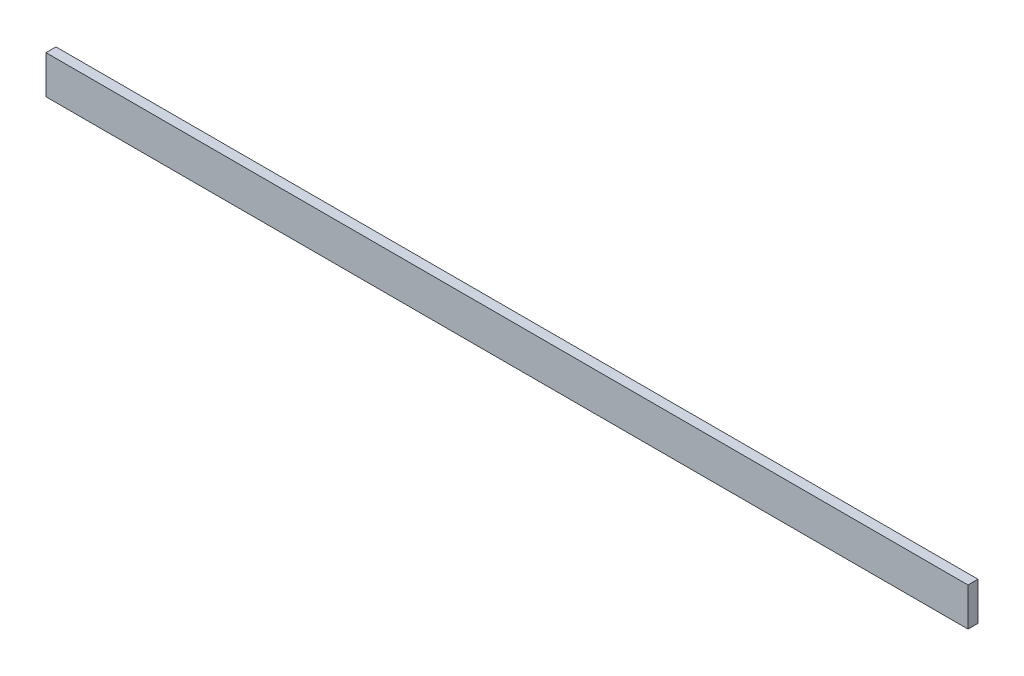
SolidWorks part; units mm, degrees
ref_plane "Front Plane" through (0, 0, 0) normal (0, 0, 1) x (1, 0, 0)
ref_plane "Top Plane" through (0, 0, 0) normal (0, 1, 0) x (1, 0, 0)
ref_plane "Right Plane" through (0, 0, 0) normal (1, 0, 0) x (0, 0, -1)
sketch "Sketch1" plane through (0, 0, 0) normal (0, 0, 1) x (1, 0, 0)
  line L0 (0, 0) -> (923.1856, 0)
  line L1 (923.1856, 0) -> (923.1856, 38.2926)
  line L2 (923.1856, 38.2926) -> (0, 38.2926)
  line L3 (0, 38.2926) -> (0, 0)
extrude "Boss-Extrude1" add sketch "Sketch1" along normal blind 10
